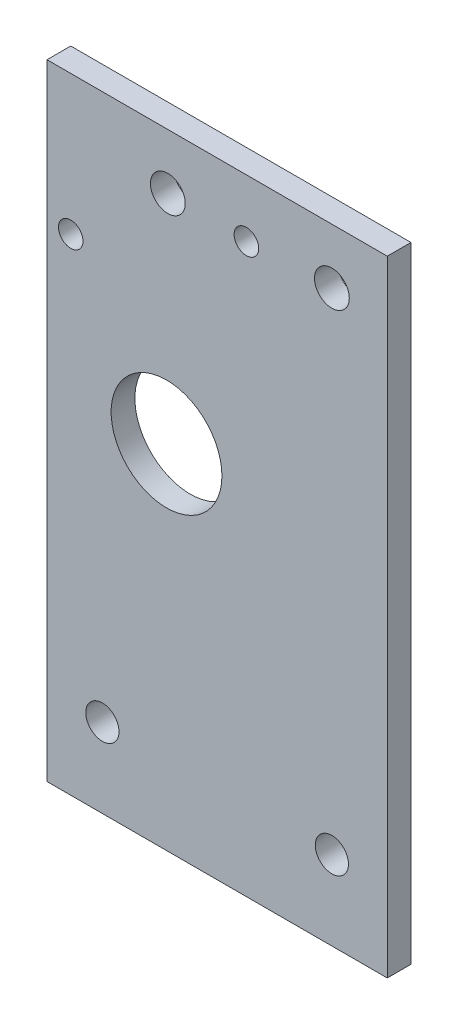
SolidWorks part; units mm, degrees
ref_plane "正面" through (0, 0, 0) normal (0, 0, 1) x (1, 0, 0)
ref_plane "平面" through (0, 0, 0) normal (0, 1, 0) x (1, 0, 0)
ref_plane "右側面" through (0, 0, 0) normal (1, 0, 0) x (0, 0, -1)
sketch "ｽｹｯﾁ1" plane through (0, 0, 0) normal (0, 0, 1) x (1, 0, 0)
  line L1 (-20, 14.5) -> (20, 14.5)
  line L2 (-20, 14.5) -> (-20, -14.5)
  line L3 (-20, -14.5) -> (20, -14.5)
  line L4 (20, 14.5) -> (20, -14.5)
  line L5 (-20, 14.5) -> (20, -14.5) construction
  line L6 (-20, -14.5) -> (20, 14.5) construction
  point P0 (0, 0)
  dimension "D1" = 40
  dimension "D2" = 29
extrude "ﾎﾞｽ - 押し出し1" add sketch "ｽｹｯﾁ1" along normal blind 3
sketch "ｽｹｯﾁ2" plane through (0, 0, 3) normal (0, 0, 1) x (1, 0, 0)
  line L1 (-20, 14.5) -> (-16.5, 14.5)
  line L2 (-20, 14.5) -> (-20, 10.5)
  line L3 (-20, 10.5) -> (-16.5, 10.5)
  line L4 (-16.5, 14.5) -> (-16.5, 10.5)
  line L5 (-20, -14.5) -> (-16.5, -14.5)
  line L6 (-20, -14.5) -> (-20, -10.5)
  line L7 (-20, -10.5) -> (-16.5, -10.5)
  line L8 (-16.5, -14.5) -> (-16.5, -10.5)
  line L9 (20, -14.5) -> (16.5, -14.5)
  line L10 (20, -14.5) -> (20, -10.5)
  line L11 (20, -10.5) -> (16.5, -10.5)
  line L12 (16.5, -14.5) -> (16.5, -10.5)
  line L13 (20, 14.5) -> (16.5, 14.5)
  line L14 (20, 14.5) -> (20, 10.5)
  line L15 (20, 10.5) -> (16.5, 10.5)
  line L16 (16.5, 14.5) -> (16.5, 10.5)
  circle A0 centre (-16.5, 10.5) radius 2.1
  circle A1 centre (-16.5, -10.5) radius 2.1
  circle A2 centre (16.5, -10.5) radius 2.1
  circle A3 centre (16.5, 10.5) radius 2.1
  dimension "D9" = 4.2
  dimension "D10" = 4.2
  dimension "D11" = 4.2
  dimension "D12" = 4.2
  dimension "D1" = 3.5
  dimension "D2" = 4
  dimension "D3" = 3.5
  dimension "D4" = 4
  dimension "D5" = 3.5
  dimension "D6" = 4
  dimension "D7" = 3.5
  dimension "D8" = 4
extrude "ｶｯﾄ - 押し出し1" cut sketch "ｽｹｯﾁ2" against normal blind 3 contours L3 A0 L4 | L4 A0 L3 | L8 A1 L7 | L7 A1 L8 | L12 A2 L11 | L11 A2 L12 | L16 A3 L15 | L15 A3 L16
sketch "ｽｹｯﾁ3" plane through (0, -14.5, 0) normal (0, -1, 0) x (1, 0, 0)
  line L1 (20, 0) -> (-20, 0)
  line L2 (20, 0) -> (20, 3)
  line L3 (20, 3) -> (-20, 3)
  line L4 (-20, 0) -> (-20, 3)
extrude "ﾎﾞｽ - 押し出し2" add sketch "ｽｹｯﾁ3" along normal blind 10
sketch "ｽｹｯﾁ4" plane through (0, 14.5, 0) normal (0, 1, 0) x (1, 0, 0)
  line L1 (20, -3) -> (-20, -3)
  line L2 (20, -3) -> (20, 0)
  line L3 (20, 0) -> (-20, 0)
  line L4 (-20, -3) -> (-20, 0)
extrude "ﾎﾞｽ - 押し出し3" add sketch "ｽｹｯﾁ4" along normal blind 10
sketch "ｽｹｯﾁ6" plane through (20, 0, 0) normal (1, 0, 0) x (0, 0, -1)
  line L1 (0, 24.5) -> (-3, 24.5)
  line L2 (0, 24.5) -> (0, -24.5)
  line L3 (0, -24.5) -> (-3, -24.5)
  line L4 (-3, 24.5) -> (-3, -24.5)
extrude "ﾎﾞｽ - 押し出し5" add sketch "ｽｹｯﾁ6" along normal blind 42
sketch "ｽｹｯﾁ7" plane through (0, 0, 3) normal (0, 0, 1) x (1, 0, 0)
  line L0 (62, 0) -> (43.1058, 0)
  line L1 (62, 24.5) -> (62, -24.5) construction
  line L2 (43.1058, 0) -> (36.1058, 0)
  line L7 (31.9689, -11.1369) -> (54.2427, 11.1369) construction
  line L8 (31.9689, 11.1369) -> (54.2427, -11.1369) construction
  line L9 (43.1058, 0) -> (29.4659, 7.875)
  line L10 (43.1058, 0) -> (43.1058, 15.75)
  line L11 (43.1058, 0) -> (56.7457, 7.875)
  line L12 (43.1058, 0) -> (29.4659, -7.875)
  line L13 (43.1058, 0) -> (43.1058, -15.75)
  line L14 (43.1058, 0) -> (56.7457, -7.875)
  circle A0 centre (43.1058, 0) radius 15.75
  circle A6 centre (43.1058, 15.75) radius 1.75
  circle A7 centre (29.4659, -7.875) radius 1.75
  circle A8 centre (43.1058, -15.75) radius 1.75
  circle A9 centre (56.7457, -7.875) radius 1.75
  circle A10 centre (56.7457, 7.875) radius 1.75
  circle A11 centre (36.1058, 0) radius 7
  dimension "D3" = 60
  dimension "D4" = 7
  dimension "D5" = 60
  dimension "D6" = 60
  dimension "D7" = 31.5
  dimension "D9" = 3.5
  dimension "D10" = 3.5
  dimension "D11" = 3.5
  dimension "D12" = 3.5
  dimension "D13" = 3.5
  dimension "D14" = 14
  dimension "D2" = 60
sketch "ｽｹｯﾁ8" plane through (-20, 0, 0) normal (-1, 0, 0) x (0, 0, 1)
  line L1 (3, -24.5) -> (0, -24.5)
  line L2 (3, -24.5) -> (3, 24.5)
  line L3 (3, 24.5) -> (0, 24.5)
  line L4 (0, -24.5) -> (0, 24.5)
extrude "ﾎﾞｽ - 押し出し6" add sketch "ｽｹｯﾁ8" along normal blind 2
sketch "ｽｹｯﾁ9" plane through (62, 0, 0) normal (1, 0, 0) x (0, 0, -1)
  line L1 (0, 24.5) -> (-3, 24.5)
  line L2 (0, 24.5) -> (0, -24.5)
  line L3 (0, -24.5) -> (-3, -24.5)
  line L4 (-3, 24.5) -> (-3, -24.5)
extrude "ﾎﾞｽ - 押し出し7" add sketch "ｽｹｯﾁ9" along normal blind 2
sketch "ｽｹｯﾁ10" plane through (0, -24.5, 0) normal (0, -1, 0) x (1, 0, 0)
  line L1 (-22, 0) -> (64, 0)
  line L2 (-22, 0) -> (-22, 3)
  line L3 (-22, 3) -> (64, 3)
  line L4 (64, 0) -> (64, 3)
extrude "ﾎﾞｽ - 押し出し8" add sketch "ｽｹｯﾁ10" along normal blind 10
sketch "ｽｹｯﾁ11" plane through (0, 24.5, 0) normal (0, 1, 0) x (1, 0, 0)
  line L1 (-22, 0) -> (64, 0)
  line L2 (-22, 0) -> (-22, -3)
  line L3 (-22, -3) -> (64, -3)
  line L4 (64, 0) -> (64, -3)
extrude "ﾎﾞｽ - 押し出し9" add sketch "ｽｹｯﾁ11" along normal blind 10
extrude "ｶｯﾄ - 押し出し4" cut sketch "ｽｹｯﾁ7" against normal blind 10
sketch "ｽｹｯﾁ14" plane through (-22, 0, 0) normal (-1, 0, 0) x (0, 0, 1)
  line L0 (0, 34.5) -> (0, -34.5) construction
  line L1 (3, -34.5) -> (0, -34.5)
  line L2 (3, -34.5) -> (3, 34.5)
  line L3 (3, 34.5) -> (0, 34.5)
  line L4 (0, -34.5) -> (0, 34.5)
  line L5 (0, 34.5) -> (3, 34.5) construction
extrude "ｶｯﾄ - 押し出し5" cut sketch "ｽｹｯﾁ14" against normal blind 43
sketch "ｽｹｯﾁ17" plane through (0, -34.5, 0) normal (0, -1, 0) x (1, 0, 0)
  line L1 (21, 3) -> (64, 3)
  line L2 (21, 3) -> (21, 0)
  line L3 (21, 0) -> (64, 0)
  line L4 (64, 3) -> (64, 0)
extrude "ﾎﾞｽ - 押し出し10" add sketch "ｽｹｯﾁ17" along normal blind 20
sketch "ｽｹｯﾁ18" plane through (0, 0, 3) normal (0, 0, 1) x (1, 0, 0)
  line L0 (21, -54.5) -> (21, -34.5)
  line L1 (21, -54.5) -> (21, 34.5) construction
  line L3 (64, -54.5) -> (64, -34.5)
  line L4 (64, 34.5) -> (64, -54.5) construction
  line L5 (64, -34.5) -> (57, -34.5)
  line L6 (21, -34.5) -> (28, -34.5)
  circle A0 centre (28, -34.5) radius 2.1
  circle A1 centre (57, -34.5) radius 2.1
  dimension "D5" = 4.2
  dimension "D6" = 4.2
  dimension "D1" = 20
  dimension "D2" = 20
  dimension "D3" = 7
  dimension "D4" = 7
extrude "ｶｯﾄ - 押し出し6" cut sketch "ｽｹｯﾁ18" against normal blind 10
sketch "ｽｹｯﾁ19" plane through (0, 0, 3) normal (0, 0, 1) x (1, 0, 0)
  line L0 (42.5, -54.5) -> (42.5, 34.5)
  line L1 (64, -54.5) -> (21, -54.5) construction
  line L2 (21, 34.5) -> (64, 34.5) construction
  circle A0 centre (28, -34.5) radius 2.1 construction
  circle A1 centre (57, -34.5) radius 2.1 construction
  dimension "D2" = 14.5
  dimension "D1" = 14.5
sketch "ｽｹｯﾁ20" plane through (0, -54.5, 0) normal (0, -1, 0) x (1, 0, 0)
  line L1 (64, 0) -> (21, 0)
  line L2 (64, 0) -> (64, 3)
  line L3 (64, 3) -> (21, 3)
  line L4 (21, 0) -> (21, 3)
extrude "ﾎﾞｽ - 押し出し11" add sketch "ｽｹｯﾁ20" along normal blind 10
sketch "ｽｹｯﾁ21" plane through (0, -64.5, 0) normal (0, -1, 0) x (1, 0, 0)
  line L1 (21, 3) -> (64, 3)
  line L2 (21, 3) -> (21, 0)
  line L3 (21, 0) -> (64, 0)
  line L4 (64, 3) -> (64, 0)
extrude "ｶｯﾄ - 押し出し7" cut sketch "ｽｹｯﾁ21" against normal blind 20
sketch "ｽｹｯﾁ22" plane through (0, 0, 3) normal (0, 0, 1) x (1, 0, 0)
  circle A0 centre (29.4659, 7.875) radius 1.75
sketch "ｽｹｯﾁ24" plane through (0, 0, 0) normal (0, 0, -1) x (-1, 0, 0)
  line L0 (-42.5, 34.5) -> (-36.27, 34.5)
  line L1 (-64, 34.5) -> (-21, 34.5) construction
  line L2 (-36.27, 34.5) -> (-36.27, 27.5)
  line L3 (-64, 34.5) -> (-64, 27.5)
  line L4 (-64, -44.5) -> (-64, 34.5) construction
  line L5 (-64, 27.5) -> (-57, 27.5)
  circle A0 centre (-36.27, 27.5) radius 2.2
  circle A1 centre (-57, 27.5) radius 2.2
  dimension "D6" = 4.4
  dimension "D7" = 4.4
  dimension "D1" = 6.23
  dimension "D2" = 7
  dimension "D3" = 7
  dimension "D4" = 0
  dimension "D5" = 7
extrude "ｶｯﾄ - 押し出し8" cut sketch "ｽｹｯﾁ24" against normal blind 30
sketch "ｽｹｯﾁ25" plane through (0, 0, 0) normal (0, 0, -1) x (-1, 0, 0)
  line L0 (-21, 34.5) -> (-21, 31.5)
  line L1 (-21, 34.5) -> (-21, -44.5) construction
  line L2 (-21, 31.5) -> (-24, 31.5)
  line L3 (-24, 31.5) -> (-24, 16.9055)
  line L4 (-24, 16.9055) -> (-46.2, 16.9055)
  line L5 (-46.2, 16.9055) -> (-46.2, 27.2055)
  circle A0 centre (-24, 16.9055) radius 1.55
  circle A1 centre (-46.2, 27.2055) radius 1.55
  dimension "D5" = 3.1
  dimension "D6" = 3.1
  dimension "D1" = 3
  dimension "D2" = 3
  dimension "D3" = 22.2
  dimension "D4" = 10.3
extrude "ｶｯﾄ - 押し出し11" cut sketch "ｽｹｯﾁ25" against normal through all both and the other way through all
